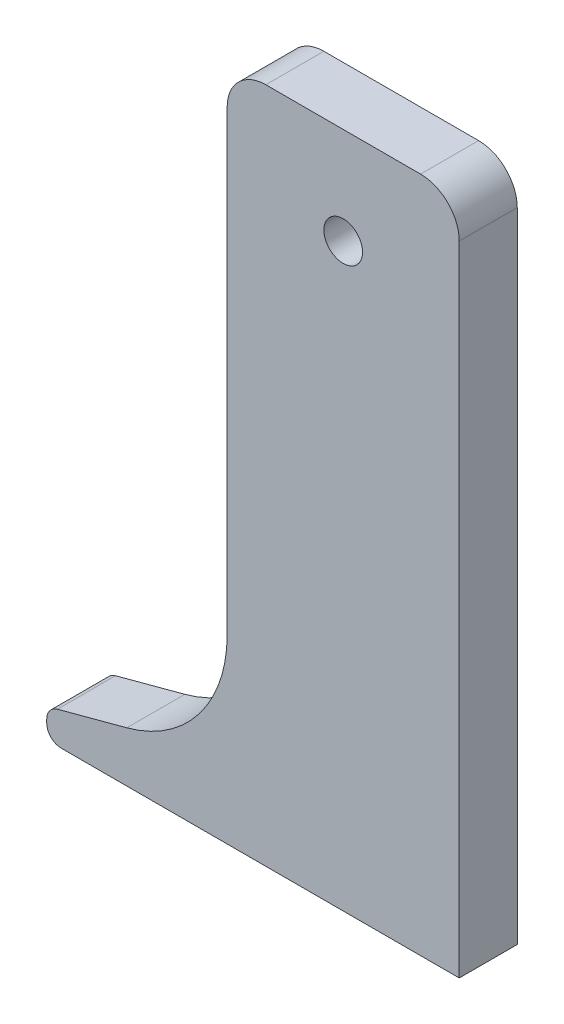
SolidWorks part; units mm, degrees
ref_plane "Front Plane" through (0, 0, 0) normal (0, 0, 1) x (1, 0, 0)
ref_plane "Top Plane" through (0, 0, 0) normal (0, 1, 0) x (1, 0, 0)
ref_plane "Right Plane" through (0, 0, 0) normal (1, 0, 0) x (0, 0, -1)
sketch "Sketch1" plane through (0, 0, 0) normal (0, 0, 1) x (1, 0, 0)
  line L0 (-6, -30) -> (-14.5801, -30)
  line L6 (-6, 0) -> (-6, -20.6287)
  line L7 (-6, -30) -> (6, -30)
  line L8 (6, 0) -> (6, -30)
  line L9 (-15.3301, -29.25) -> (-15.3301, -29.0755)
  line L10 (-14.7742, -28.3511) -> (-11.1883, -27.3902)
  line L13 (-6, 0) -> (-6, 3)
  line L14 (-4, 5) -> (4, 5)
  line L15 (6, 0) -> (6, 3)
  arc A0 (-11.1883, -27.3902) -> (-6, -20.6287) centre (-13, -20.6287) ccw
  arc A1 (-15.3301, -29.0755) -> (-14.7742, -28.3511) centre (-14.5801, -29.0755) cw
  arc A2 (-14.5801, -30) -> (-15.3301, -29.25) centre (-14.5801, -29.25) cw
  arc A3 (4, 5) -> (6, 3) centre (4, 3) cw
  arc A4 (-6, 3) -> (-4, 5) centre (-4, 3) cw
  point P4 (0, 5)
  point P7 (6, 5)
  point P14 (-6, -26)
  point P17 (-15.3301, -28.5)
  point P20 (-15.3301, -30)
  point P27 (-6, 5)
  dimension "D4" = 7
  dimension "D7" = 0.75
  dimension "D8" = 0.75
  dimension "D12" = 2
  dimension "D1" = 12
  dimension "D2" = 30
  dimension "D3" = 1.5
  dimension "D5" = 75
  dimension "D6" = 4
  dimension "D9" = 5
  dimension "D10" = 12
  dimension "D11" = 5
extrude "Boss-Extrude1" add sketch "Sketch1" along normal blind 3
sketch "Sketch2" plane through (0, 0, 3) normal (0, 0, 1) x (1, 0, 0)
  circle A0 centre (0, 0) radius 1
  dimension "D1" = 2
extrude "Cut-Extrude1" cut sketch "Sketch2" against normal through all both and the other way through all
